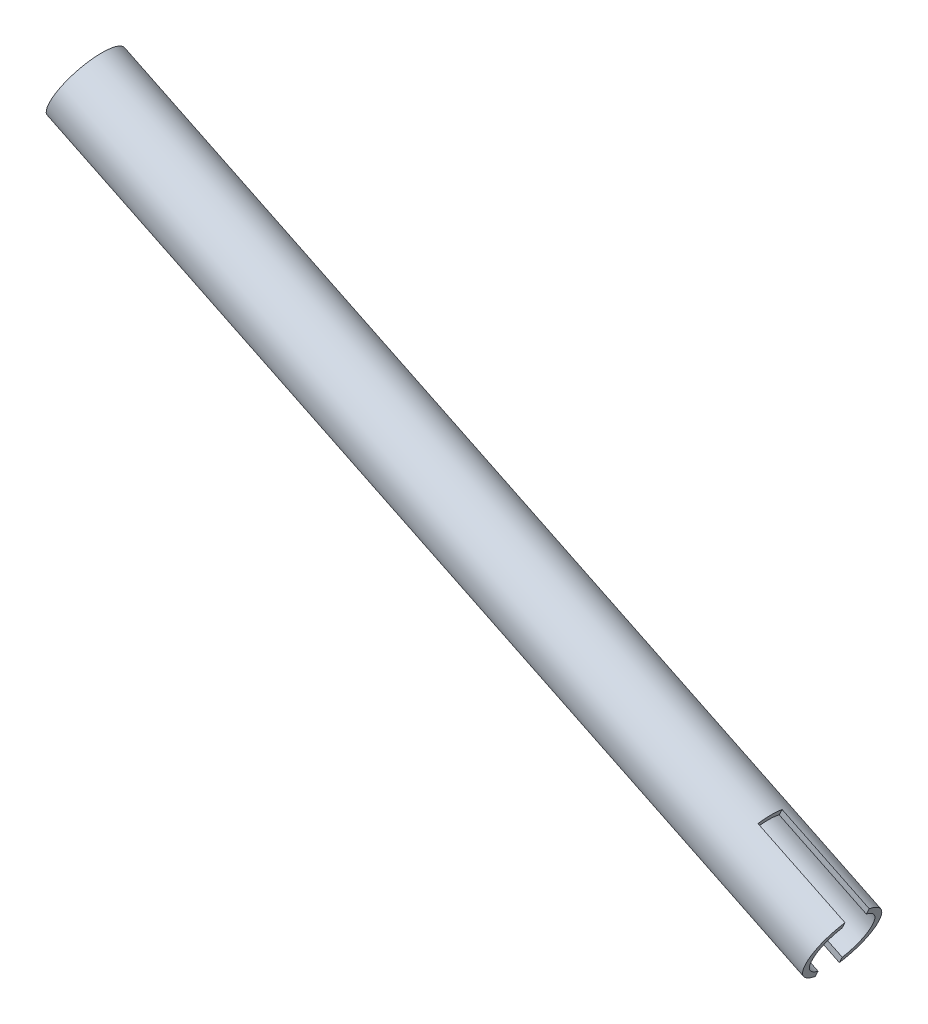
SolidWorks part; units mm, degrees
ref_plane "Front" through (0, 0, 0) normal (0, 0, 1) x (1, 0, 0)
ref_plane "Top" through (0, 0, 0) normal (0, 1, 0) x (1, 0, 0)
ref_plane "Right" through (0, 0, 0) normal (1, 0, 0) x (0, 0, -1)
sketch "Sketch1" plane through (0, 0, 0) normal (0, 0, 1) x (1, 0, 0)
  line L0 (369.4422, 123.8028) -> (567.8647, 27.3461)
  line L1 (567.8647, 27.3461) -> (567.1429, 25.8613)
  line L2 (567.1429, 25.8613) -> (368.7203, 122.318)
  line L3 (368.7203, 122.318) -> (369.4422, 123.8028)
  line L5 (328.6246, 152.4) -> (628.4169, 6.6657) construction
  line L6 (549.9184, 44.8252) -> (569.1037, 35.4989) construction
  dimension "D1" = 1.651
  dimension "D2" = 9.525
revolve "Revolve1" add sketch "Sketch1" angle 360 about L6
sketch "Sketch2" plane through (0, 0, 0) normal (0, 0, 1) x (1, 0, 0)
  line L0 (552.6276, 54.099) -> (575.4715, 42.9942)
  line L1 (575.4715, 42.9942) -> (567.1429, 25.8613)
  line L2 (567.1429, 25.8613) -> (544.299, 36.9661)
  line L3 (544.299, 36.9661) -> (552.6276, 54.099)
  line L4 (575.4715, 42.9942) -> (377.049, 139.4509) construction
  line L5 (368.7203, 122.318) -> (567.1429, 25.8613) construction
  line L6 (550.9064, 50.5582) -> (553.6826, 56.2692) construction
  line L7 (567.8647, 27.3461) -> (574.7497, 41.5093) construction
extrude "Cut-Extrude1" cut sketch "Sketch2" against normal up to surface and the other way up to surface
move or copy body "Body-Move/Copy1" [suppressed] bodies to move or copy 102
equation "\"D1@Sketch1\"=\"a arm tube thickness@FS2-SU-RS-A-0002-V1, REAR LEFT SUSPENSION.Assembly\""
equation "\"D2@Sketch1\"=\"a arm tube diameter@FS2-SU-RS-A-0002-V1, REAR LEFT SUSPENSION.Assembly\"/2"
